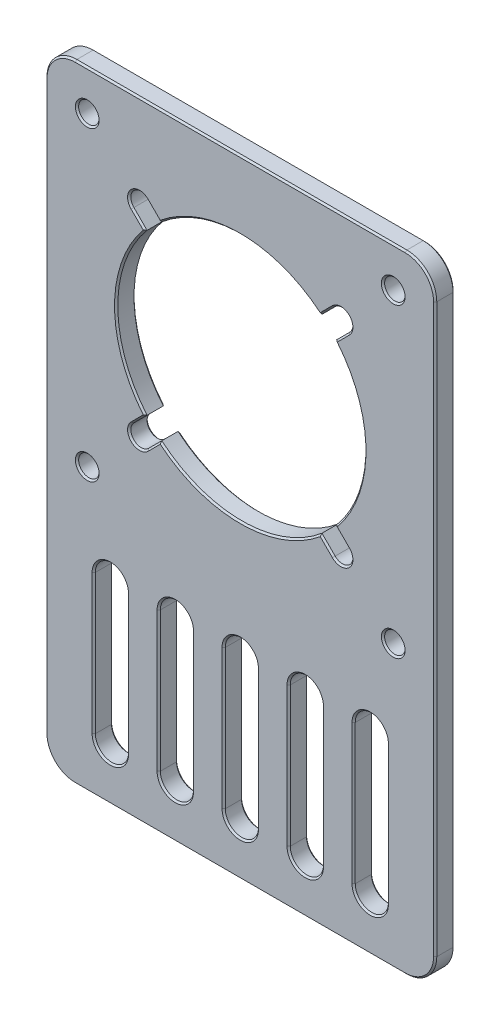
SolidWorks part; units mm, degrees
ref_plane "Front Plane" through (0, 0, 0) normal (0, 0, 1) x (1, 0, 0)
ref_plane "Top Plane" through (0, 0, 0) normal (0, 1, 0) x (1, 0, 0)
ref_plane "Right Plane" through (0, 0, 0) normal (1, 0, 0) x (0, 0, -1)
sketch "Эскиз1" plane through (0, 0, 0) normal (0, 0, 1) x (1, 0, 0)
  line L1 (-25.4, -48.25) -> (25.4, -48.25)
  line L2 (-30, -43.65) -> (-30, 43.65)
  line L3 (-25.4, 48.25) -> (25.4, 48.25)
  line L4 (30, -43.65) -> (30, 43.65)
  line L7 (-30, 18.55) -> (30, 18.55) construction
  line L16 (-30, -18.7) -> (30, -18.7) construction
  line L17 (23.55, -5) -> (-23.55, -5) construction
  line L18 (23.55, -5) -> (23.55, 42.1) construction
  line L19 (23.55, 42.1) -> (-23.55, 42.1) construction
  line L20 (-23.55, -5) -> (-23.55, 42.1) construction
  line L23 (-30, -40.2) -> (30, -40.2) construction
  line L24 (-20, -18.7) -> (-20, -40.2) construction
  line L25 (-12.55, -40.2) -> (-12.55, -18.7)
  line L27 (-22.55, -40.2) -> (-22.55, -18.7)
  line L29 (-17.45, -40.2) -> (-17.45, -18.7)
  line L30 (-22.55, -40.2) -> (-17.45, -18.7) construction
  line L31 (-22.55, -18.7) -> (-17.45, -40.2) construction
  line L32 (-7.45, -40.2) -> (-7.45, -18.7)
  line L33 (-10, -18.7) -> (-10, -40.2) construction
  line L34 (-12.55, -40.2) -> (-7.45, -18.7) construction
  line L35 (-12.55, -18.7) -> (-7.45, -40.2) construction
  line L36 (-2.55, -40.2) -> (-2.55, -18.7)
  line L37 (2.55, -40.2) -> (2.55, -18.7)
  line L38 (0, -18.7) -> (0, -40.2) construction
  line L39 (-2.55, -40.2) -> (2.55, -18.7) construction
  line L40 (-2.55, -18.7) -> (2.55, -40.2) construction
  line L41 (7.45, -40.2) -> (7.45, -18.7)
  line L42 (12.55, -40.2) -> (12.55, -18.7)
  line L43 (10, -18.7) -> (10, -40.2) construction
  line L44 (7.45, -40.2) -> (12.55, -18.7) construction
  line L45 (7.45, -18.7) -> (12.55, -40.2) construction
  line L46 (17.45, -40.2) -> (17.45, -18.7)
  line L47 (22.55, -40.2) -> (22.55, -18.7)
  line L48 (20, -18.7) -> (20, -40.2) construction
  line L49 (17.45, -40.2) -> (22.55, -18.7) construction
  line L50 (17.45, -18.7) -> (22.55, -40.2) construction
  line L56 (-16.6214, 32.9086) -> (-14.5896, 30.8769)
  line L57 (-14.3586, 35.1714) -> (-12.3269, 33.1396)
  line L60 (14.3586, 35.1714) -> (12.3269, 33.1396)
  line L61 (16.6214, 32.9086) -> (14.5896, 30.8769)
  line L62 (14.5896, 6.2231) -> (16.6214, 4.1914)
  line L63 (12.3269, 3.9604) -> (14.3586, 1.9286)
  line L64 (-14.5896, 6.2231) -> (-16.6214, 4.1914)
  line L66 (-12.3269, 3.9604) -> (-14.3586, 1.9286)
  arc A0 (-14.5896, 30.8769) -> (-14.5896, 6.2231) centre (0, 18.55) ccw
  arc A1 (-17.45, -18.7) -> (-22.55, -18.7) centre (-20, -18.7) ccw
  arc A2 (-22.55, -40.2) -> (-17.45, -40.2) centre (-20, -40.2) ccw
  arc A3 (-7.45, -18.7) -> (-12.55, -18.7) centre (-10, -18.7) ccw
  arc A4 (-12.55, -40.2) -> (-7.45, -40.2) centre (-10, -40.2) ccw
  arc A5 (2.55, -18.7) -> (-2.55, -18.7) centre (0, -18.7) ccw
  arc A6 (-2.55, -40.2) -> (2.55, -40.2) centre (0, -40.2) ccw
  arc A7 (12.55, -18.7) -> (7.45, -18.7) centre (10, -18.7) ccw
  arc A8 (7.45, -40.2) -> (12.55, -40.2) centre (10, -40.2) ccw
  arc A9 (22.55, -18.7) -> (17.45, -18.7) centre (20, -18.7) ccw
  arc A10 (17.45, -40.2) -> (22.55, -40.2) centre (20, -40.2) ccw
  arc A11 (-25.4, -48.25) -> (-30, -43.65) centre (-25.4, -43.65) cw
  arc A12 (25.4, -48.25) -> (30, -43.65) centre (25.4, -43.65) ccw
  arc A13 (30, 43.65) -> (25.4, 48.25) centre (25.4, 43.65) ccw
  arc A14 (-30, 43.65) -> (-25.4, 48.25) centre (-25.4, 43.65) cw
  arc A16 (-14.3586, 35.1714) -> (-16.6214, 32.9086) centre (-15.49, 34.04) ccw
  arc A17 (14.3586, 35.1714) -> (16.6214, 32.9086) centre (15.49, 34.04) cw
  arc A18 (14.3586, 1.9286) -> (16.6214, 4.1914) centre (15.49, 3.06) ccw
  arc A19 (-14.3586, 1.9286) -> (-16.6214, 4.1914) centre (-15.49, 3.06) cw
  arc A20 (12.3269, 33.1396) -> (-12.3269, 33.1396) centre (0, 18.55) ccw
  arc A21 (14.5896, 6.2231) -> (14.5896, 30.8769) centre (0, 18.55) ccw
  arc A22 (-12.3269, 3.9604) -> (12.3269, 3.9604) centre (0, 18.55) ccw
  point P0 (0, 0)
  point P22 (-20, -29.45)
  point P31 (-10, -29.45)
  point P38 (0, -29.45)
  point P45 (10, -29.45)
  point P52 (20, -29.45)
  dimension "D4" = 66.95
  dimension "D9" = 4.6
  dimension "D3" = 29.7
  dimension "D5" = 88.45
  dimension "D6" = 10
  dimension "D7" = 5.1
  dimension "D8" = 5
extrude "Бобышка-Вытянуть1" add sketch "Эскиз1" along normal blind 3
hole_wizard "Сверло под метчик  спиральное M31" positions "Эскиз2" profile "Эскиз3" hole size "M3x0.5" standard "DIN" end condition through all
sketch "Эскиз2" plane through (0, 0, 3) normal (0, 0, 1) x (1, 0, 0)
  point P0 (-23.55, 42.1)
  point P3 (23.55, 42.1)
  point P6 (23.55, -5)
  point P9 (-23.55, -5)
sketch "Эскиз3" plane through (-23.55, 42.1, 3) normal (1, 0, 0) x (0, -1, 0)
  line L0 (0, 0) -> (0, 3)
  line L1 (0, 3) -> (1.575, 3)
  line L2 (1.575, 3) -> (1.575, 0)
  line L5 (1.575, 0) -> (0, 0)
  line L11 (0, -6.35) -> (0, 107.95) construction
  dimension "Диаметр сквозного отверстия" = 3.15
  dimension "Глубина сквозного отверстия" = 3
chamfer "Фаска2" distance 0.25 angle 45 96 edges at (17.45, -29.45, 3) (20, -42.75, 3) (22.55, -29.45, 3) (20, -16.15, 3) (-2.55, -29.45, 3) (0, -42.75, 3) (2.55, -29.45, 3) (0, -16.15, 3) (-22.55, -29.45, 3) (-20, -42.75, 3) (-17.45, -29.45, 3) (-20, -16.15, 3) (-30, 0, 3) (-28.6527, 46.9027, 3) (0, 48.25, 3) (28.6527, 46.9027, 3) (30, 0, 3) (28.6527, -46.9027, 3) (0, -48.25, 3) (-28.6527, -46.9027, 3) (15.6055, 31.8928, 3) (16.6214, 35.1714, 3) (13.3428, 34.1555, 3) (0, 37.65, 3) (-13.3428, 34.1555, 3) (-16.6214, 35.1714, 3) (-15.6055, 31.8928, 3) (-19.1, 18.55, 3) (-15.6055, 5.2072, 3) (-16.6214, 1.9286, 3) (-13.3428, 2.9445, 3) (0, -0.55, 3) (13.3428, 2.9445, 3) (16.6214, 1.9286, 3) (15.6055, 5.2072, 3) (19.1, 18.55, 3) (-12.55, -29.45, 3) (-10, -42.75, 3) (-7.45, -29.45, 3) (-10, -16.15, 3) (7.45, -29.45, 3) (10, -42.75, 3) (12.55, -29.45, 3) (10, -16.15, 3) (-21.975, -5, 3) (25.125, -5, 3) (25.125, 42.1, 3) (-21.975, 42.1, 3) (20, -42.75, 0) (17.45, -29.45, 0) (20, -16.15, 0) (22.55, -29.45, 0) (10, -42.75, 0) (7.45, -29.45, 0) (10, -16.15, 0) (12.55, -29.45, 0) (0, -42.75, 0) (-2.55, -29.45, 0) (0, -16.15, 0) (2.55, -29.45, 0) (-10, -42.75, 0) (-12.55, -29.45, 0) (-10, -16.15, 0) (-7.45, -29.45, 0) (-20, -42.75, 0) (-22.55, -29.45, 0) (-20, -16.15, 0) (-17.45, -29.45, 0) (16.6214, 1.9286, 0) (13.3428, 2.9445, 0) (0, -0.55, 0) (-13.3428, 2.9445, 0) (-16.6214, 1.9286, 0) (-15.6055, 5.2072, 0) (-19.1, 18.55, 0) (-15.6055, 31.8928, 0) (-16.6214, 35.1714, 0) (-13.3428, 34.1555, 0) (0, 37.65, 0) (13.3428, 34.1555, 0) (16.6214, 35.1714, 0) (15.6055, 31.8928, 0) (19.1, 18.55, 0) (15.6055, 5.2072, 0) (0, -48.25, 0) (28.6527, -46.9027, 0) (30, 0, 0) (28.6527, 46.9027, 0) (0, 48.25, 0) (-28.6527, 46.9027, 0) (-30, 0, 0) (-28.6527, -46.9027, 0) (-21.975, -5, 0) (25.125, -5, 0) (25.125, 42.1, 0) (-21.975, 42.1, 0)
